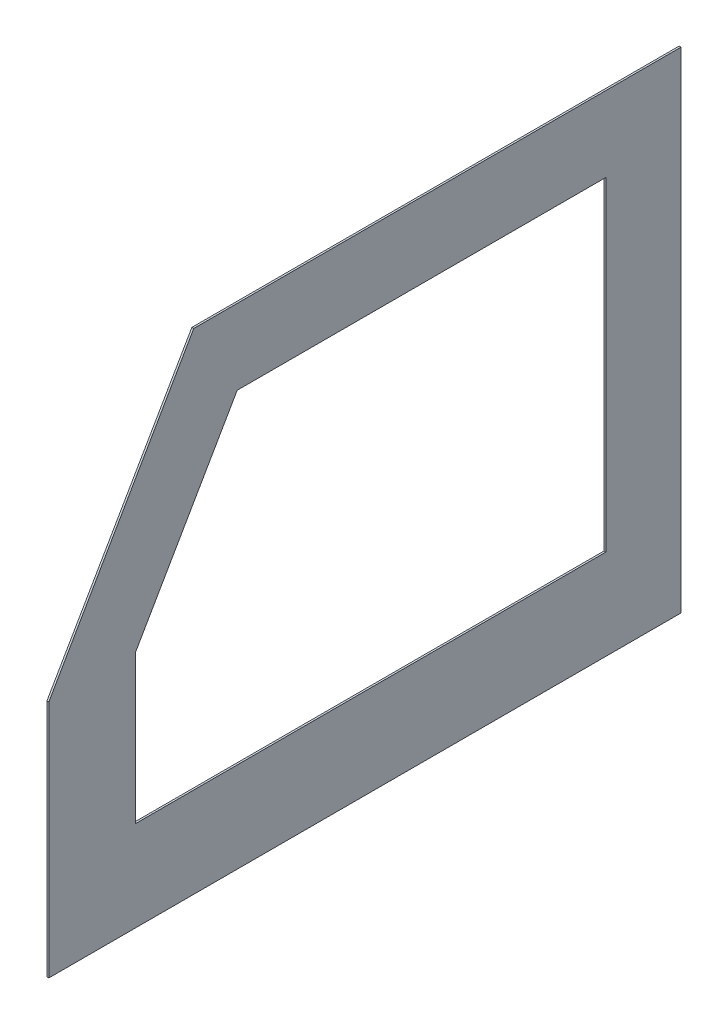
SolidWorks part; units mm, degrees
ref_plane "Front Plane" through (0, 0, 0) normal (0, 0, 1) x (1, 0, 0)
ref_plane "Top Plane" through (0, 0, 0) normal (0, 1, 0) x (1, 0, 0)
ref_plane "Right Plane" through (0, 0, 0) normal (1, 0, 0) x (0, 0, -1)
sketch "Sketch1" plane through (0, 0, 0) normal (1, 0, 0) x (0, 0, -1)
  line L0 (0, 0) -> (-822.2662, 0)
  line L1 (-822.2662, 0) -> (-1066.8, -423.545)
  line L2 (-1066.8, -423.545) -> (-1066.8, -826.77)
  line L3 (-1066.8, -826.77) -> (0, -826.77)
  line L4 (0, -826.77) -> (0, 0)
  dimension "D1" = 826.77
  dimension "D2" = 1066.8
  dimension "D3" = 30
  dimension "D4" = 403.225
  dimension "D5" = 822.2662
extrude "Boss-Extrude1" add sketch "Sketch1" along normal blind 3.175
sketch "Sketch2" plane through (3.175, 0, 0) normal (1, 0, 0) x (0, 0, -1)
  line L0 (-748.9427, -127) -> (-920.153, -423.545)
  line L1 (-920.153, -423.545) -> (-127, -423.545) construction
  line L2 (-127, -423.545) -> (-127, -127)
  line L3 (-127, -127) -> (-748.9427, -127)
  line L4 (0, -826.77) -> (0, 0) construction
  line L5 (0, 0) -> (-822.2662, 0) construction
  line L6 (-822.2662, 0) -> (-1066.8, -423.545) construction
  line L7 (-920.153, -423.545) -> (-920.153, -674.37)
  line L8 (-920.153, -674.37) -> (-127, -674.37)
  line L9 (-127, -674.37) -> (-127, -423.545)
  line L10 (-1066.8, -826.77) -> (0, -826.77) construction
  dimension "D1" = 127
  dimension "D2" = 127
  dimension "D3" = 127
  dimension "D4" = 403.225
  dimension "D5" = 152.4
extrude "Cut-Extrude1" cut sketch "Sketch2" against normal up to next
